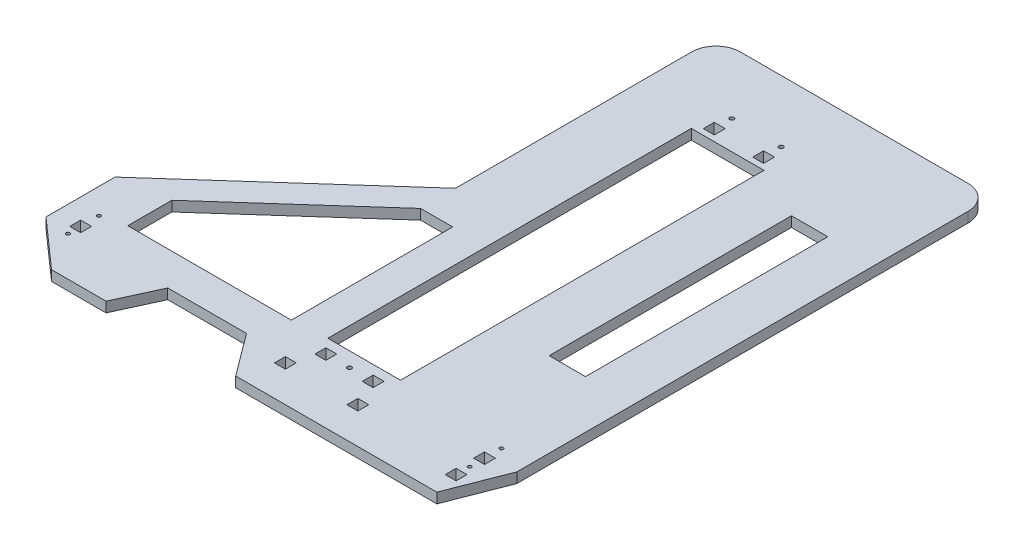
SolidWorks part; units mm, degrees
ref_plane "Front Plane" through (0, 0, 0) normal (0, 0, 1) x (1, 0, 0)
ref_plane "Top Plane" through (0, 0, 0) normal (0, 1, 0) x (1, 0, 0)
ref_plane "Right Plane" through (0, 0, 0) normal (1, 0, 0) x (0, 0, -1)
sketch "Sketch1" plane through (0, 0, 0) normal (0, 1, 0) x (1, 0, 0)
  line L0 (0, 0) -> (-228, 0)
  line L1 (-228, 0) -> (-228, -215)
  line L2 (-228, -215) -> (-376.5, -347.4717)
  line L3 (-376.5, -347.4717) -> (-376.5, -404.4717)
  line L4 (-376.5, -404.4717) -> (-336.5, -439.9)
  line L5 (-336.5, -439.9) -> (-291.5, -439.9)
  line L6 (-291.5, -439.9) -> (-275.5, -405)
  line L7 (-275.5, -405) -> (-210.5, -405)
  line L8 (-210.5, -405) -> (-184.5, -439.9)
  line L9 (-184.5, -439.9) -> (-18.5, -439.9)
  line L10 (-18.5, -439.9) -> (0, -392.4)
  line L11 (0, -392.4) -> (0, 0)
  line L12 (-291.5, -439.9) -> (-184.5, -439.9) construction
  dimension "D1" = 45
  dimension "D2" = 65
  dimension "D3" = 228
  dimension "D4" = 215
  dimension "D5" = 57
  dimension "D6" = 18.5
  dimension "D7" = 34.9
  dimension "D8" = 166
  dimension "D9" = 47.5
  dimension "D10" = 16
  dimension "D11" = 26
  dimension "D12" = 40
  dimension "D13" = 190
  dimension "D14" = 199
extrude "Boss-Extrude1" add sketch "Sketch1" along normal blind 8.4
sketch "Sketch2" plane through (0, 8.4, 0) normal (0, 1, 0) x (1, 0, 0)
  line L0 (-228, -215) -> (-228, -405) construction
  line L1 (-275.5, -405) -> (-210.5, -405) construction
  line L2 (-336.5, -439.9) -> (-336.5, -311.7891) construction
  line L3 (-228, -215) -> (-376.5, -347.4717) construction
  line L4 (-336.5, -340.6005) -> (-228, -243.8114)
  line L5 (-228, -243.8114) -> (-201.5, -243.8114)
  line L6 (-201.5, -243.8114) -> (-201.5, -377)
  line L7 (-201.5, -377) -> (-336.5, -377)
  line L8 (-336.5, -377) -> (-336.5, -340.6005)
  line L9 (-184.5, -439.9) -> (-18.5, -439.9) construction
  line L10 (-173.5, -374.9) -> (-113.5, -374.9)
  line L11 (-173.5, -374.9) -> (-173.5, -74.9)
  line L12 (-173.5, -74.9) -> (-113.5, -74.9)
  line L13 (-113.5, -374.9) -> (-113.5, -74.9)
  line L15 (-23.1, -439.9) -> (-23.1, 0) construction
  line L16 (0, 0) -> (-228, 0) construction
  line L17 (-355.4, -423.1601) -> (-355.4, -328.6491) construction
  line L18 (-27.6, -423.9) -> (-18.6, -423.9)
  line L19 (-27.6, -423.9) -> (-27.6, -414.9)
  line L20 (-27.6, -414.9) -> (-18.6, -414.9)
  line L21 (-18.6, -423.9) -> (-18.6, -414.9)
  line L22 (-27.6, -423.9) -> (-18.6, -414.9) construction
  line L23 (-27.6, -414.9) -> (-18.6, -423.9) construction
  line L24 (-27.6, -400.45) -> (-18.6, -400.45)
  line L25 (-27.6, -400.45) -> (-27.6, -391.45)
  line L26 (-27.6, -391.45) -> (-18.6, -391.45)
  line L27 (-18.6, -400.45) -> (-18.6, -391.45)
  line L28 (-27.6, -400.45) -> (-18.6, -391.45) construction
  line L29 (-27.6, -391.45) -> (-18.6, -400.45) construction
  line L30 (-376.5, -404.4717) -> (-336.5, -439.9) construction
  line L31 (-376.5, -347.4717) -> (-376.5, -404.4717) construction
  line L32 (-350.9, -392.4717) -> (-359.9, -392.4717)
  line L33 (-350.9, -392.4717) -> (-350.9, -401.4717)
  line L34 (-350.9, -401.4717) -> (-359.9, -401.4717)
  line L35 (-359.9, -392.4717) -> (-359.9, -401.4717)
  line L36 (-350.9, -392.4717) -> (-359.9, -401.4717) construction
  line L37 (-350.9, -401.4717) -> (-359.9, -392.4717) construction
  line L39 (0, -392.4) -> (0, 0) construction
  line L40 (-173.024, -65.6) -> (-113.024, -65.6) construction
  line L41 (-143.5, -74.9) -> (-143.5, -65.6) construction
  line L42 (-168.35, -61.1) -> (-159.35, -61.1)
  line L43 (-168.35, -61.1) -> (-168.35, -70.1)
  line L44 (-168.35, -70.1) -> (-159.35, -70.1)
  line L45 (-159.35, -61.1) -> (-159.35, -70.1)
  line L46 (-168.35, -61.1) -> (-159.35, -70.1) construction
  line L47 (-168.35, -70.1) -> (-159.35, -61.1) construction
  line L48 (-118.65, -70.1) -> (-127.65, -61.1) construction
  line L49 (-118.65, -61.1) -> (-127.65, -70.1) construction
  line L50 (-127.65, -61.1) -> (-127.65, -70.1)
  line L51 (-118.65, -70.1) -> (-127.65, -70.1)
  line L52 (-118.65, -61.1) -> (-118.65, -70.1)
  line L53 (-118.65, -61.1) -> (-127.65, -61.1)
  line L54 (-163.85, -65.6) -> (-163.85, -51.1) construction
  line L55 (-123.15, -65.6) -> (-123.15, -51.1) construction
  line L56 (-143.5, -374.9) -> (-143.5, -439.9) construction
  line L57 (-163, -387) -> (-124, -387) construction
  line L58 (-119.5, -391.5) -> (-128.5, -382.5) construction
  line L59 (-167.5, -382.5) -> (-158.5, -382.5)
  line L60 (-167.5, -382.5) -> (-167.5, -391.5)
  line L61 (-167.5, -391.5) -> (-158.5, -391.5)
  line L62 (-158.5, -382.5) -> (-158.5, -391.5)
  line L63 (-167.5, -382.5) -> (-158.5, -391.5) construction
  line L64 (-167.5, -391.5) -> (-158.5, -382.5) construction
  line L65 (-119.5, -382.5) -> (-128.5, -391.5) construction
  line L66 (-128.5, -382.5) -> (-128.5, -391.5)
  line L67 (-119.5, -391.5) -> (-128.5, -391.5)
  line L68 (-119.5, -382.5) -> (-119.5, -391.5)
  line L69 (-119.5, -382.5) -> (-128.5, -382.5)
  line L70 (-109.1, -414.5) -> (-118.1, -405.5) construction
  line L71 (-177.9, -405.5) -> (-168.9, -405.5)
  line L72 (-177.9, -405.5) -> (-177.9, -414.5)
  line L73 (-177.9, -414.5) -> (-168.9, -414.5)
  line L74 (-168.9, -405.5) -> (-168.9, -414.5)
  line L75 (-177.9, -405.5) -> (-168.9, -414.5) construction
  line L76 (-177.9, -414.5) -> (-168.9, -405.5) construction
  line L77 (-109.1, -405.5) -> (-118.1, -414.5) construction
  line L78 (-118.1, -405.5) -> (-118.1, -414.5)
  line L79 (-109.1, -414.5) -> (-118.1, -414.5)
  line L80 (-109.1, -405.5) -> (-109.1, -414.5)
  line L81 (-109.1, -405.5) -> (-118.1, -405.5)
  circle A0 centre (-23.1, -408.2) radius 1.5
  circle A1 centre (-23.1, -382) radius 1.5
  circle A2 centre (-355.4, -407.3717) radius 1.5
  circle A3 centre (-355.4, -381.7717) radius 1.5
  circle A4 centre (-163.85, -51.1) radius 1.75
  circle A5 centre (-123.15, -51.1) radius 1.75
  circle A6 centre (-143.5, -387) radius 1.75
  point P25 (-23.1, -419.4)
  point P30 (-23.1, -395.95)
  point P44 (-355.4, -396.9717)
  point P61 (-163.85, -65.6)
  point P72 (-123.15, -65.6)
  point P85 (-163, -387)
  point P94 (-124, -387)
  point P95 (-173.4, -410)
  point P104 (-113.6, -410)
  dimension "D13" = 3
  dimension "D14" = 3
  dimension "D23" = 3
  dimension "D24" = 3
  dimension "D31" = 3.5
  dimension "D34" = 3.5
  dimension "D1" = 21.5
  dimension "D2" = 28
  dimension "D3" = 26.5
  dimension "D4" = 60
  dimension "D5" = 300
  dimension "D6" = 65
  dimension "D7" = 28
  dimension "D8" = 9
  dimension "D9" = 9
  dimension "D10" = 9
  dimension "D11" = 9
  dimension "D12" = 23.45
  dimension "D15" = 26.2
  dimension "D16" = 11.2
  dimension "D17" = 16
  dimension "D18" = 18.6
  dimension "D19" = 9
  dimension "D20" = 9
  dimension "D21" = 3
  dimension "D22" = 16.6
  dimension "D25" = 25.6
  dimension "D26" = 10.4
  dimension "D27" = 9
  dimension "D28" = 9
  dimension "D29" = 31.7
  dimension "D30" = 4.8
  dimension "D32" = 10
  dimension "D33" = 9
  dimension "D35" = 39
  dimension "D36" = 7.6
  dimension "D37" = 0
  dimension "D38" = 9
  dimension "D39" = 9
  dimension "D40" = 10.4
  dimension "D41" = 23
extrude "Cut-Extrude1" cut sketch "Sketch2" against normal through all
fillet "Fillet1" radius 20 2 edges at (0, 4.2, 0) (-228, 4.2, 0)
sketch "Sketch3" plane through (0, 8.4, 0) normal (0, 1, 0) x (1, 0, 0)
  line L0 (-53.5, 0) -> (-53.5, -439.9) construction
  line L1 (-20, 0) -> (-208, 0) construction
  line L2 (-184.5, -439.9) -> (-18.5, -439.9) construction
  line L3 (-113.5, -74.9) -> (-173.5, -74.9) construction
  line L4 (-113.5, -374.9) -> (-113.5, -74.9) construction
  line L6 (-93.5, -284.9) -> (-13.5, -284.9)
  line L7 (-93.5, -284.9) -> (-93.5, -174.9)
  line L8 (-93.5, -174.9) -> (-13.5, -174.9)
  line L9 (-13.5, -284.9) -> (-13.5, -174.9)
  line L10 (-93.5, -284.9) -> (-13.5, -174.9) construction
  line L11 (-93.5, -174.9) -> (-13.5, -284.9) construction
  circle A0 centre (-53.5, -114.9) radius 30
  point P8 (-143.5, -74.9)
  point P13 (-53.5, -229.9)
  dimension "D1" = 60
  dimension "D2" = 40
  dimension "D3" = 60
  dimension "D4" = 80
  dimension "D5" = 110
  dimension "D6" = 60
extrude "Cut-Extrude2" [suppressed] cut sketch "Sketch3" against normal through all
sketch "Sketch4" plane through (0, 8.4, 0) normal (0, 1, 0) x (1, 0, 0)
  line L1 (-69.7351, -95.9937) -> (-39.7351, -95.9937)
  line L2 (-69.7351, -95.9937) -> (-69.7351, -295.9937)
  line L3 (-69.7351, -295.9937) -> (-39.7351, -295.9937)
  line L4 (-39.7351, -95.9937) -> (-39.7351, -295.9937)
  line L5 (-69.7351, -95.9937) -> (-39.7351, -295.9937) construction
  line L6 (-69.7351, -295.9937) -> (-39.7351, -95.9937) construction
  point P0 (-54.7351, -195.9937)
  dimension "D1" = 30
  dimension "D2" = 200
extrude "Cut-Extrude3" cut sketch "Sketch4" against normal through all
